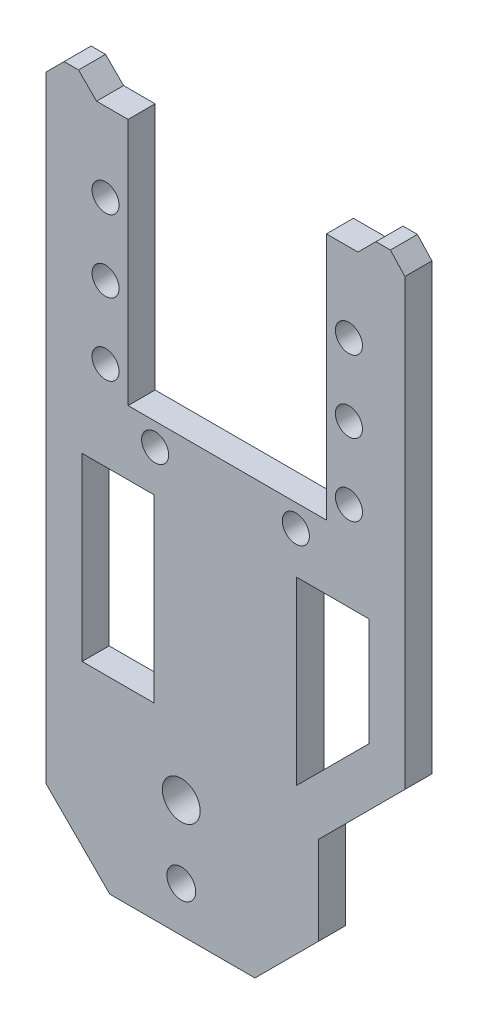
SolidWorks part; units mm, degrees
ref_plane "Ön Düzlem" through (0, 0, 0) normal (0, 0, 1) x (1, 0, 0)
ref_plane "Üst Düzlem" through (0, 0, 0) normal (0, 1, 0) x (1, 0, 0)
ref_plane "Sağ Düzlem" through (0, 0, 0) normal (1, 0, 0) x (0, 0, -1)
ref_plane "Düzlem1" through (0, 0, 3) normal (0, 0, 1) x (1, 0, 0)
sketch "Çizim1" plane through (0, 0, 3) normal (0, 0, 1) x (1, 0, 0)
  line L0 (-20.1, -15) -> (-20.1, -83.3848)
  line L1 (-20.1, -83.3848) -> (-13.0289, -90.4559)
  line L2 (-13.0289, -90.4559) -> (3.0758, -90.4559)
  line L3 (3.0758, -90.4559) -> (10.1468, -83.3848)
  line L4 (10.1468, -83.3848) -> (10.1468, -73.5865)
  line L5 (10.1468, -73.5865) -> (19.7099, -64.0235)
  line L6 (19.7099, -14.7401) -> (19.7099, -64.0235)
  line L9 (18.1, -13) -> (16.5, -13)
  line L10 (16.5, -13) -> (14.5, -15)
  line L11 (14.5, -15) -> (14.5, -41.5)
  line L12 (13.5, -42.5) -> (-13.5, -42.5)
  line L13 (-14.5, -41.5) -> (-14.5, -15)
  line L14 (-14.5, -15) -> (-16.5, -13)
  line L15 (-16.5, -13) -> (-18.1, -13)
  line L16 (-18.1, -13) -> (-20.1, -15)
  line L17 (19.7099, -14.7401) -> (18.1, -13)
  circle A0 centre (-5.1, -77.4559) radius 2.1
  circle A1 centre (-5.1, -85.4559) radius 1.6
  arc A2 (14.5, -41.5) -> (13.5, -42.5) centre (13.5, -41.5) cw
  arc A3 (-13.5, -42.5) -> (-14.5, -41.5) centre (-13.5, -41.5) cw
  dimension "D1" = 3.2
  dimension "D2" = 8
  dimension "D3" = 4.2
  dimension "D4" = 0
  dimension "D5" = 15
  dimension "D6" = 5
  dimension "D9" = 10
  dimension "D10" = 10
extrude "Yükseklik-Ekstrüzyon1" add sketch "Çizim1" against normal blind 3
sketch "Çizim4" plane through (0, 0, 3) normal (0, 0, 1) x (1, 0, 0)
  line L0 (13.5, -42.5) -> (-13.5, -42.5) construction
  line L1 (-16.5, -13) -> (-14.5, -15)
  line L2 (-16.5, -13) -> (-16.5, -43.1474)
  line L3 (-16.5, -43.1474) -> (16.5, -43.1474)
  line L4 (16.5, -13) -> (16.5, -43.1474)
  line L5 (-14.5, -15) -> (-11, -15)
  line L7 (-11, -42.5) -> (11, -42.5)
  line L12 (-11, -15) -> (-11, -42.5)
  line L13 (16.5, -13) -> (14.5, -15)
  line L14 (14.5, -15) -> (11, -15)
  line L15 (11, -15) -> (11, -42.5)
extrude "Yükseklik-Ekstrüzyon2" add sketch "Çizim4" against normal up to surface (3 mm away) up to face at (-3.5, -85.4559, 0)
sketch "Çizim5" plane through (0, 0, 0) normal (0, 0, -1) x (-1, 0, 0)
  line L0 (-14.5, -15) -> (-11, -15) construction
  line L1 (-11, -15) -> (-11, -42.5) construction
  line L2 (-11, -42.5) -> (11, -42.5) construction
  line L4 (-19.7099, -64.0235) -> (-19.7099, -14.7401) construction
  circle A0 centre (-13.5, -23.75) radius 1.5
  circle A1 centre (-13.5, -31.75) radius 1.5
  circle A2 centre (-13.5, -39.75) radius 1.5
  circle A3 centre (-7.6099, -45) radius 1.5
  circle A4 centre (8, -45) radius 1.5
  circle A5 centre (13.5, -39.75) radius 1.5
  circle A6 centre (13.5, -31.75) radius 1.5
  circle A7 centre (13.5, -23.75) radius 1.5
  dimension "D1" = 3
  dimension "D2" = 8.75
  dimension "D3" = 2.5
  dimension "D4" = 3
  dimension "D5" = 3
  dimension "D6" = 8
  dimension "D7" = 8
  dimension "D8" = 2.5
  dimension "D9" = 3
  dimension "D10" = 12.1
  dimension "D11" = 3
  dimension "D12" = 3
  dimension "D13" = 3
  dimension "D14" = 3
  dimension "D15" = 3
extrude "Kes-Ekstrüzyon1" cut sketch "Çizim5" against normal blind 4
sketch "Sketch3" plane through (0, 0, 0) normal (0, 0, -1) x (-1, 0, 0)
  line L0 (16.1, -49.6334) -> (8.1, -49.6334)
  line L1 (-15.7099, -49.6334) -> (-15.7099, -61.6334)
  line L2 (-15.7099, -61.6334) -> (-7.7099, -69.6334)
  line L3 (-7.7099, -69.6334) -> (-7.7099, -49.6334)
  line L4 (16.1, -49.6334) -> (16.1, -69.6334)
  line L5 (16.1, -69.6334) -> (8.1, -69.6334)
  line L6 (20.1, -15) -> (20.1, -83.3848) construction
  line L7 (8.1, -69.6334) -> (8.1, -49.6334)
  line L8 (-7.7099, -49.6334) -> (-15.7099, -49.6334)
  line L10 (-19.7099, -64.0235) -> (-19.7099, -14.7401) construction
  dimension "D1" = 20
  dimension "D2" = 135
  dimension "D3" = 8
  dimension "D4" = 4
  dimension "D5" = 4
  dimension "D6" = 8
  dimension "D7" = 20
extrude "Cut-Extrude1" cut sketch "Sketch3" against normal blind 10
